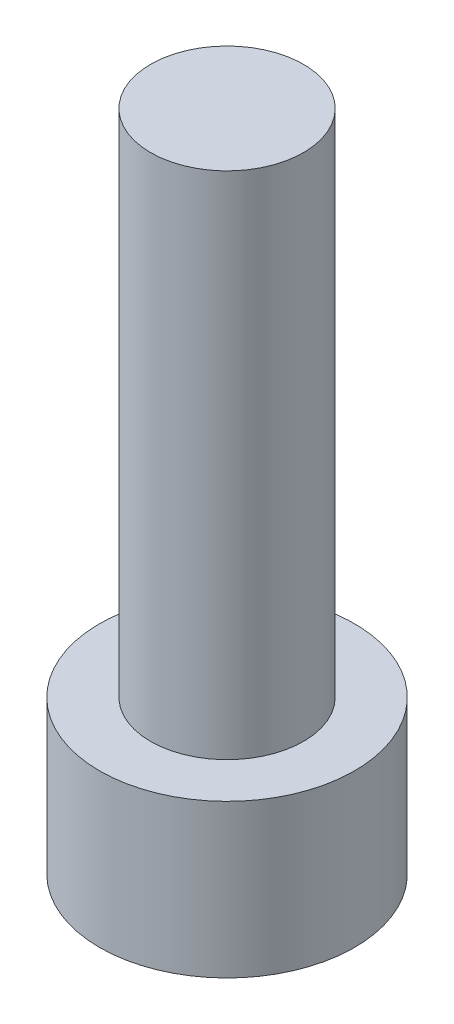
SolidWorks part; units mm, degrees
ref_plane "前视基准面" through (0, 0, 0) normal (0, 0, 1) x (1, 0, 0)
ref_plane "上视基准面" through (0, 0, 0) normal (0, 1, 0) x (1, 0, 0)
ref_plane "右视基准面" through (0, 0, 0) normal (1, 0, 0) x (0, 0, -1)
sketch "草图1" plane through (0, 0, 0) normal (0, 1, 0) x (1, 0, 0)
  circle A0 centre (0, 0) radius 2.5
  dimension "D1" = 5
extrude "凸台-拉伸1" add sketch "草图1" along normal blind 3
sketch "草图2" plane through (0, 3, 0) normal (0, 1, 0) x (1, 0, 0)
  circle A0 centre (0, 0) radius 1.5
extrude "凸台-拉伸2" add sketch "草图2" along normal blind 10
sketch "草图3" plane through (0, 0, 0) normal (0, -1, 0) x (1, 0, 0)
  line L1 (1.425, 0) -> (0.7125, 1.2341)
  line L2 (0.7125, 1.2341) -> (-0.7125, 1.2341)
  line L3 (-0.7125, 1.2341) -> (-1.425, 0)
  line L4 (-1.425, 0) -> (-0.7125, -1.2341)
  line L5 (-0.7125, -1.2341) -> (0.7125, -1.2341)
  line L6 (0.7125, -1.2341) -> (1.425, 0)
  circle A0 centre (0, 0) radius 1.2341 construction
extrude "切除-拉伸1" cut sketch "草图3" against normal blind 1.65
